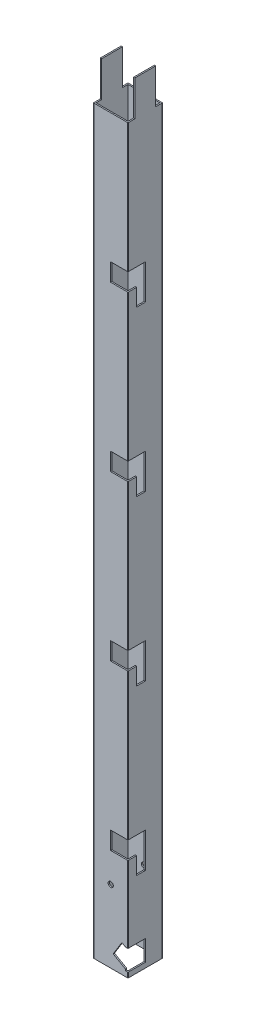
SolidWorks part; units mm, degrees
ref_plane "Front Plane" through (0, 0, 0) normal (0, 0, 1) x (1, 0, 0)
ref_plane "Top Plane" through (0, 0, 0) normal (0, 1, 0) x (1, 0, 0)
ref_plane "Right Plane" through (0, 0, 0) normal (1, 0, 0) x (0, 0, -1)
sketch "Sketch1" plane through (0, 0, 0) normal (0, 1, 0) x (1, 0, 0)
  line L0 (1.5, 1.5) -> (38.5, 1.5)
  line L1 (0.5, 0) -> (39.5, 0)
  line L2 (0, 0.5) -> (0, 39.5)
  line L3 (0.5, 40) -> (39.5, 40)
  line L4 (40, 0.5) -> (40, 39.5)
  line L5 (38.5, 1.5) -> (38.5, 38.5)
  line L6 (1.5, 38.5) -> (38.5, 38.5)
  line L7 (1.5, 1.5) -> (1.5, 38.5)
  arc A0 (39.5, 0) -> (40, 0.5) centre (39.5, 0.5) ccw
  arc A1 (0.5, 0) -> (0, 0.5) centre (0.5, 0.5) cw
  arc A2 (0, 39.5) -> (0.5, 40) centre (0.5, 39.5) cw
  arc A3 (39.5, 40) -> (40, 39.5) centre (39.5, 39.5) cw
  arc A4 (38.5, 1.5) -> (38.5, 1.5) centre (38.5, 1.5) ccw
  arc A5 (38.5, 38.5) -> (38.5, 38.5) centre (38.5, 38.5) cw
  arc A6 (1.5, 38.5) -> (1.5, 38.5) centre (1.5, 38.5) cw
  arc A7 (1.5, 1.5) -> (1.5, 1.5) centre (1.5, 1.5) cw
  point P9 (0, 0)
  dimension "D3" = 0.5
  dimension "D1" = 40
  dimension "D2" = 40
  dimension "D4" = 1.5
extrude "Boss-Extrude1" add sketch "Sketch1" along normal blind 899
sketch "Sketch3" plane through (0, 0, 0) normal (0, 0, 1) x (1, 0, 0)
  line L0 (40, 5.9073) -> (37, 5.9073)
  line L1 (40, 899) -> (40, 0) construction
  line L2 (37, 5.9073) -> (37, 7.6398)
  line L3 (37, 7.6398) -> (22.8745, 15.7976)
  line L4 (32.9268, 32.0981) -> (22.8745, 15.7976)
  line L5 (32.9268, 32.0981) -> (32.6768, 31.6651) construction
  line L6 (32.9268, 32.0981) -> (58.9075, 17.0981) construction
  line L7 (32.9268, 32.0981) -> (37, 29.7464)
  line L8 (40, 29.7464) -> (37, 29.7464)
  line L9 (40, 29.7464) -> (40, 28.0143)
  line L10 (40, 28.0143) -> (42.4438, 26.6034) construction
  line L11 (40, 28.0143) -> (40, 5.9073)
  dimension "D1" = 3
  dimension "D2" = 3
extrude "Cut-Extrude2" cut sketch "Sketch3" against normal blind 20
sketch "Sketch4" plane through (0, 0, 0) normal (-1, 0, 0) x (0, 0, 1)
  line L1 (0, 899) -> (-8, 899)
  line L2 (0, 899) -> (0, 858)
  line L3 (0, 858) -> (-8, 858)
  line L4 (-8, 899) -> (-8, 858)
  line L5 (-40, 899) -> (-32, 899)
  line L6 (-40, 899) -> (-40, 858)
  line L7 (-40, 858) -> (-32, 858)
  line L8 (-32, 899) -> (-32, 858)
  dimension "D1" = 8
  dimension "D2" = 41
  dimension "D3" = 41
extrude "Cut-Extrude3" cut sketch "Sketch4" against normal through all
sketch "Sketch5" plane through (0, 0, -40) normal (0, 0, -1) x (-1, 0, 0)
  line L0 (-39.5, 0) -> (-0.5, 0) construction
  line L1 (-40, 858) -> (-40, 0) construction
  circle A0 centre (-30, 30) radius 3.5864
  circle A1 centre (-30, 15) radius 3.5864
  dimension "D1" = 15
  dimension "D2" = 15
  dimension "D3" = 10
extrude "Cut-Extrude4" cut sketch "Sketch5" against normal blind 10
sketch "Sketch6" plane through (40, 0, 0) normal (1, 0, 0) x (0, 0, -1)
  line L0 (0, 708.5) -> (20, 708.5)
  line L1 (0, 858) -> (0, 29.7464) construction
  line L2 (20, 708.5) -> (20, 668)
  line L3 (20, 668) -> (10, 668)
  line L4 (10, 668) -> (10, 688)
  line L5 (10, 688) -> (0, 688)
  line L6 (0, 688) -> (0, 708.5)
  line L7 (0, 518.5) -> (20, 518.5)
  line L8 (8, 858) -> (0.5, 858) construction
  line L9 (20, 518.5) -> (20, 478)
  line L10 (20, 478) -> (10, 478)
  line L11 (10, 478) -> (10, 498)
  line L12 (10, 498) -> (0, 498)
  line L13 (0, 498) -> (0, 518.5)
  line L14 (0, 328.5) -> (20, 328.5)
  line L15 (20, 328.5) -> (20, 288)
  line L16 (20, 288) -> (10, 288)
  line L17 (10, 288) -> (10, 308)
  line L18 (10, 308) -> (0, 308)
  line L19 (0, 308) -> (0, 328.5)
  line L20 (0, 138.5) -> (20, 138.5)
  line L21 (20, 138.5) -> (20, 98)
  line L22 (20, 98) -> (10, 98)
  line L23 (10, 98) -> (10, 118)
  line L24 (10, 118) -> (0, 118)
  line L25 (0, 118) -> (0, 138.5)
  point P8 (5, 688)
  dimension "D1" = 20.5
  dimension "D2" = 20
  dimension "D3" = 10
  dimension "D4" = 20
  dimension "D5" = 170
  dimension "D6" = 4
extrude "Cut-Extrude5" cut sketch "Sketch6" against normal blind 20
sketch "Sketch7" plane through (0, 0, 0) normal (0, 0, 1) x (1, 0, 0)
  line L0 (0.5, 0) -> (39.5, 0) construction
  circle A0 centre (20, 84) radius 3
  point P4 (20, 0)
  dimension "D1" = 6
  dimension "D2" = 84
extrude "Cut-Extrude6" cut sketch "Sketch7" against normal through all
